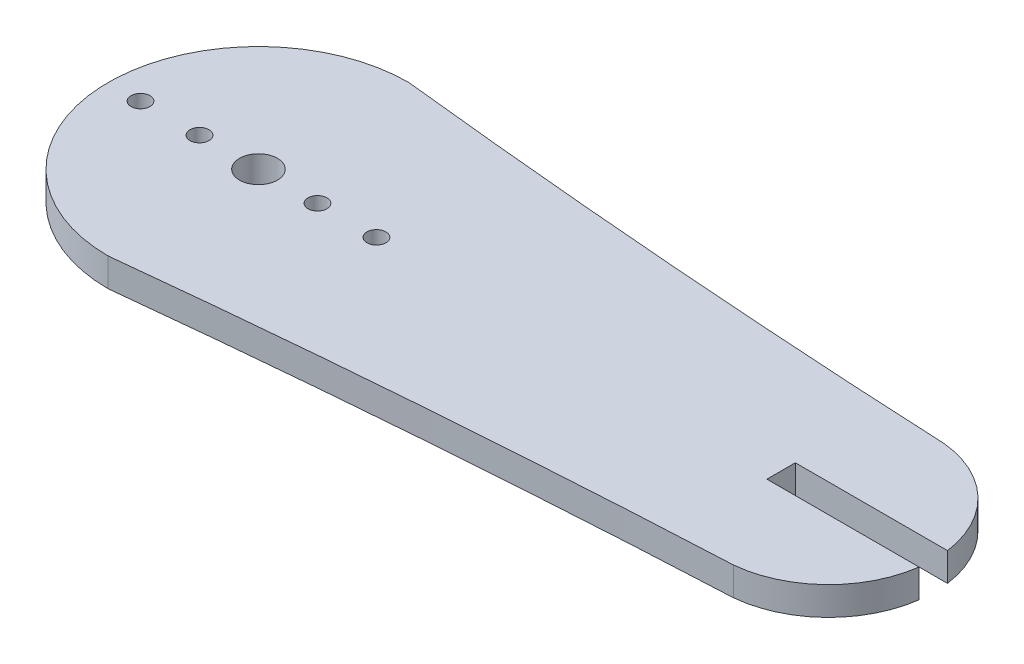
SolidWorks part; units mm, degrees
ref_plane "Front Plane" through (0, 0, 0) normal (0, 0, 1) x (1, 0, 0)
ref_plane "Top Plane" through (0, 0, 0) normal (0, 1, 0) x (1, 0, 0)
ref_plane "Right Plane" through (0, 0, 0) normal (1, 0, 0) x (0, 0, -1)
sketch "Sketch1" plane through (0, 0, 0) normal (0, 1, 0) x (1, 0, 0)
  line L1 (48.1331, -16.3404) -> (48.1331, -13.3404)
  line L3 (48.1331, -13.3404) -> (64.191, -13.3404)
  line L4 (48.1331, -16.3404) -> (64.191, -16.3404)
  circle A3 centre (-7.0224, -14.8404) radius 2
  circle A4 centre (-0.7974, -14.8404) radius 1
  circle A5 centre (5.4276, -14.8404) radius 1
  circle A6 centre (-19.4724, -14.8404) radius 1
  circle A7 centre (-13.2474, -14.8404) radius 1
  arc A8 (-3.6693, 0.6611) -> (-3.6693, -30.3419) centre (-7.0224, -14.8404) ccw
  arc A9 (53.1355, -25.9972) -> (64.191, -16.3404) centre (53.1355, -14.8404) ccw
  arc A12 (-7.0224, 1.0196) -> (54.1898, -3.7336) centre (100.965, 995.1718) ccw
  arc A15 (54.1898, -25.9473) -> (-7.0224, -30.7004) centre (100.965, -1024.8527) ccw
  arc A16 (64.191, -13.3404) -> (53.1355, -3.6837) centre (53.1355, -14.8404) ccw
  point P11 (48.1331, -23.4993)
  point P16 (-0.7974, -14.8404)
  point P17 (5.4276, -14.8404)
  point P23 (-7.0224, 1.0196)
  point P27 (-19.1224, -14.8404)
  point P28 (-13.5224, -14.8404)
  point P29 (53.1355, -3.6837)
  point P30 (53.1355, -25.9972)
  point P31 (-7.0224, -30.7004)
  dimension "D1" = 6.225
  dimension "D3" = 6.225
  dimension "D4" = 6.225
  dimension "D6" = 2
  dimension "D7" = 2
  dimension "D8" = 4
  dimension "D2" = 10
  dimension "D5" = 6.225
extrude "Boss-Extrude1" add sketch "Sketch1" along normal blind 3
